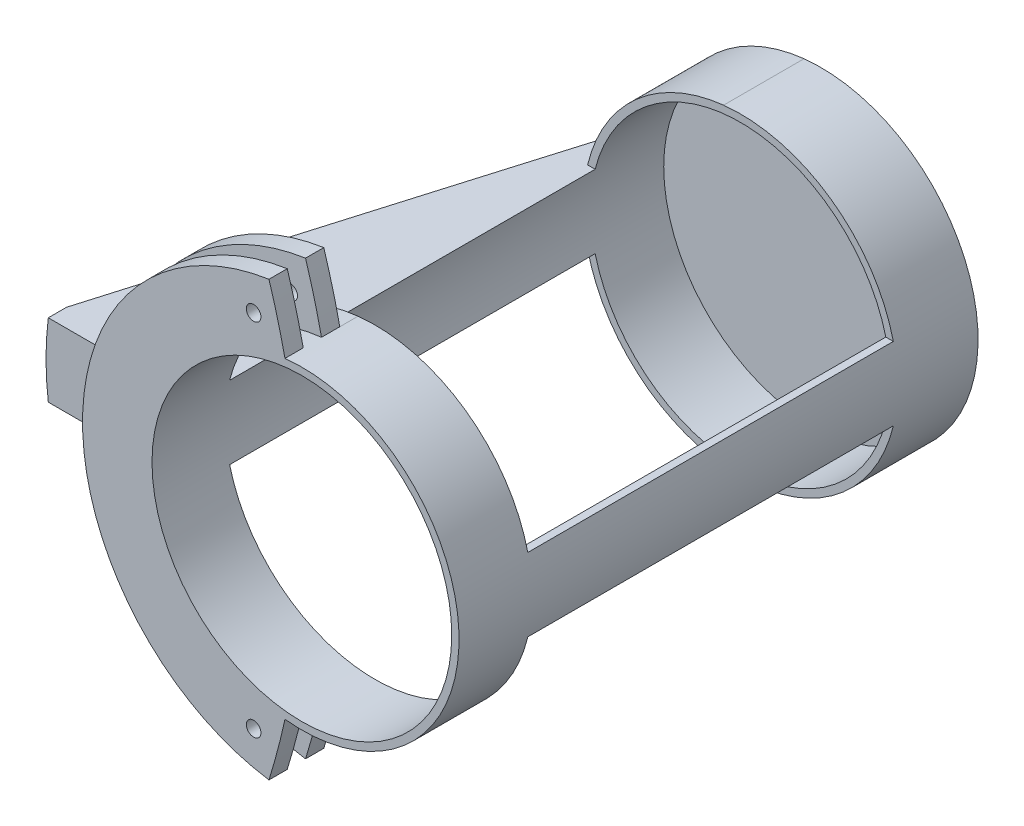
SolidWorks part; units mm, degrees
material "ABS"
ref_plane "Front Plane" through (0, 0, 0) normal (0, 0, 1) x (1, 0, 0)
ref_plane "Top Plane" through (0, 0, 0) normal (0, 1, 0) x (1, 0, 0)
ref_plane "Right Plane" through (0, 0, 0) normal (1, 0, 0) x (0, 0, -1)
sketch "Sketch1" plane through (0, 0, 0) normal (0, 0, 1) x (1, 0, 0)
  circle A0 centre (0, 0) radius 43
  dimension "D1" = 86
extrude "Boss-Extrude1" add sketch "Sketch1" along normal blind 2
sketch "Sketch2" plane through (0, 0, 2) normal (0, 0, 1) x (1, 0, 0)
  circle A0 centre (0, 0) radius 41
  circle A1 centre (0, 0) radius 43
  circle A3 centre (0, 0) radius 43 construction
  dimension "D1" = 2
extrude "Boss-Extrude2" add sketch "Sketch2" along normal blind 20
sketch "Sketch3" plane through (0, 0, 22) normal (0, 0, 1) x (1, 0, 0)
  line L0 (39.7618, 10) -> (41.821, 10)
  line L1 (-41.821, -10) -> (-39.7618, -10)
  line L3 (-41.821, 10) -> (-39.7618, 10)
  line L9 (39.7618, -10) -> (41.821, -10)
  arc A0 (-39.7618, 10) -> (-39.7618, -10) centre (0, 0) ccw
  arc A1 (-41.821, 10) -> (-41.821, -10) centre (0, 0) ccw
  circle A2 centre (0, 0) radius 41 construction
  circle A3 centre (0, 0) radius 43 construction
  arc A4 (39.7618, -10) -> (39.7618, 10) centre (0, 0) ccw
  arc A5 (41.821, -10) -> (41.821, 10) centre (0, 0) ccw
extrude "Boss-Extrude3" add sketch "Sketch3" along normal blind 100
sketch "Sketch4" plane through (0, 0, 122) normal (0, 0, 1) x (1, 0, 0)
  circle A0 centre (0, 0) radius 41
  circle A1 centre (0, 0) radius 43
  arc A2 (39.7618, -10) -> (39.7618, 10) centre (0, 0) ccw construction
  arc A3 (41.821, -10) -> (41.821, 10) centre (0, 0) ccw construction
extrude "Boss-Extrude4" add sketch "Sketch4" along normal blind 20
sketch "Sketch5" plane through (0, 0, 142) normal (0, 0, 1) x (1, 0, 0)
  line L0 (0, 0) -> (-200, 0) construction
  circle A0 centre (0, 0) radius 60
  circle A1 centre (-200, 0) radius 200
  circle A2 centre (0, 0) radius 43
  circle M4 centre (0, 0) radius 43
  dimension "D1" = 400
  dimension "D3" = 120
  dimension "D2" = 200
extrude "Boss-Extrude5" add sketch "Sketch5" against normal blind 5 contours L0 A1 A0 M4 | A2 L0 A0 A1
ref_plane "Plane1" through (0, 0, 134.5) normal (0, 0, -1) x (-1, 0, 0)
mirror "Mirror1" about plane through (0, 0, 134.5) normal (0, 0, -1) of "Boss-Extrude5"
sketch "Sketch6" plane through (0, 0, 127) normal (0, 0, -1) x (-1, 0, 0)
  line L1 (-80, -10) -> (80, -10)
  line L2 (-80, -10) -> (-80, 10)
  line L3 (-80, 10) -> (80, 10)
  line L4 (80, -10) -> (80, 10)
  line L5 (-80, -10) -> (80, 10) construction
  line L6 (-80, 10) -> (80, -10) construction
  circle A0 centre (0, 0) radius 60
  circle A1 centre (0, 0) radius 43
  point P0 (0, 0)
  arc M6 (9, -59.3212) -> (9, 59.3212) centre (0, 0) ccw
  arc M8 (4.6225, 42.7508) -> (4.6225, -42.7508) centre (0, 0) cw
  dimension "D1" = 20
  dimension "D2" = 160
extrude "Boss-Extrude6" add sketch "Sketch6" along normal up to surface (127 mm away) contours L3 L1 M8 M6 | L1 L4 L3 M6 up to face at (43, 0, 0)
sketch "Sketch7" plane through (0, 0, 0) normal (0, 1, 0) x (1, 0, 0)
  line L0 (-43, 0) -> (-80, 0)
  line L1 (-80, 0) -> (-41.821, 0) construction
  line L2 (-80, 0) -> (-80, -127)
  line L3 (-9, -127) -> (-59.1608, -127) construction
  line L4 (-80, -127) -> (-43, 0)
  line L6 (0, 46.3834) -> (0, -167.3502) construction
  line L7 (-80, 0) -> (-80, -127) construction
  line L8 (-59.1608, -127) -> (-80, -127) construction
  line L9 (-80, 0) -> (-41.821, 0) construction
  line L11 (-80, 0) -> (-87.6827, 0)
  line L12 (-80, 0) -> (-80, -127)
  line L13 (-80, -127) -> (-87.6827, -127)
  line L14 (-87.6827, 0) -> (-87.6827, -127)
  dimension "D1" = 43
revolve "Cut-Revolve1" cut sketch "Sketch7" angle 360 about L6
sketch "Sketch8" plane through (0, 0, 127) normal (0, 0, 1) x (1, 0, 0)
  line L2 (-59.1608, 10) -> (-79.3725, 10)
  line L3 (-79.3725, -10) -> (-59.1608, -10)
  line L4 (-59.1608, 10) -> (-79.3725, 10)
  line L5 (-79.3725, -10) -> (-59.1608, -10)
  arc A2 (-79.3725, 10) -> (-79.3725, -10) centre (0, 0) ccw
  arc A3 (-59.1608, 10) -> (-59.1608, -10) centre (0, 0) ccw
  arc A4 (-79.3725, 10) -> (-79.3725, -10) centre (0, 0) ccw
  arc A5 (-59.1608, 10) -> (-59.1608, -10) centre (0, 0) ccw
  dimension "D1" = 0
extrude "Boss-Extrude7" add sketch "Sketch8" along normal up to surface (5 mm away) up to face at (-29.0668, 0, 132)
sketch "Sketch10" plane through (0, 0, 142) normal (0, 0, 1) x (1, 0, 0)
  line L0 (0, 0) -> (-22.9881, 85.7927) construction
  line L1 (0, 0) -> (-24.8058, -92.5765) construction
  line L2 (0, 0) -> (-119.0369, 0) construction
  circle A0 centre (0, 0) radius 51 construction
  circle A1 centre (0, 0) radius 41 construction
  circle A2 centre (-13.1998, 49.2622) radius 2
  circle A3 centre (-13.1998, -49.2622) radius 2
  dimension "D1" = 10
  dimension "D4" = 4
  dimension "D5" = 4
  dimension "D2" = 75
  dimension "D3" = 75
extrude "Cut-Extrude2" cut sketch "Sketch10" against normal up to surface (15 mm away) up to face at (-31.9016, -34.0349, 127)
